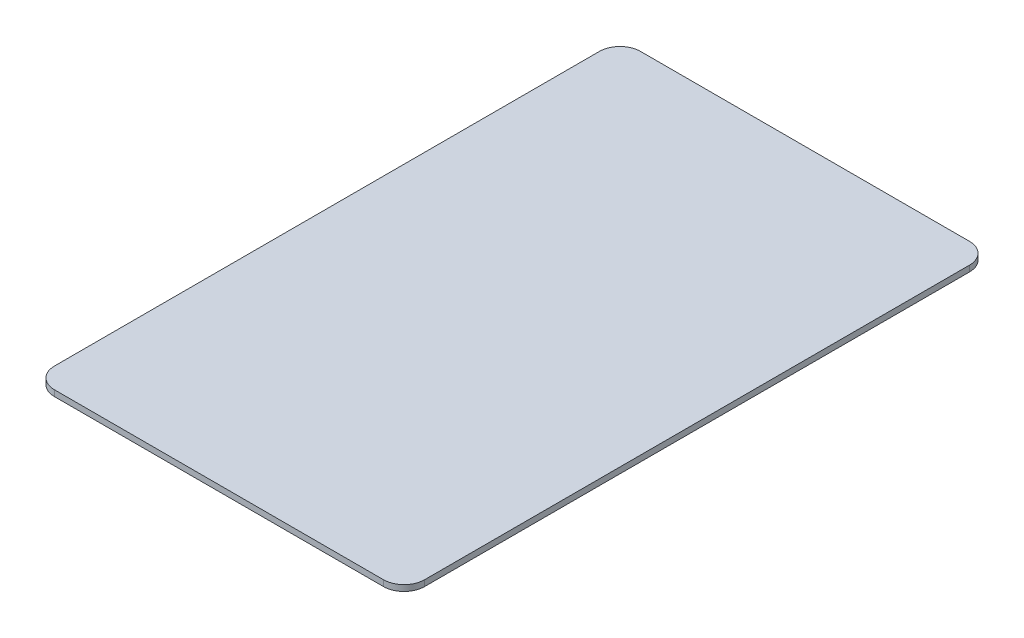
SolidWorks part; units mm, degrees
ref_plane "Front Plane" through (0, 0, 0) normal (0, 0, 1) x (1, 0, 0)
ref_plane "Top Plane" through (0, 0, 0) normal (0, 1, 0) x (1, 0, 0)
ref_plane "Right Plane" through (0, 0, 0) normal (1, 0, 0) x (0, 0, -1)
sketch "Sketch1" plane through (0, 0, 0) normal (0, 1, 0) x (1, 0, 0)
  line L1 (-24, -42.75) -> (24, -42.75)
  line L2 (-27, -39.75) -> (-27, 39.75)
  line L3 (-24, 42.75) -> (24, 42.75)
  line L4 (27, -39.75) -> (27, 39.75)
  line L5 (-27, -42.75) -> (27, 42.75) construction
  line L6 (-27, 42.75) -> (27, -42.75) construction
  arc A0 (24, 42.75) -> (27, 39.75) centre (24, 39.75) cw
  arc A1 (-24, -42.75) -> (-27, -39.75) centre (-24, -39.75) cw
  arc A2 (27, -39.75) -> (24, -42.75) centre (24, -39.75) cw
  arc A3 (-27, 39.75) -> (-24, 42.75) centre (-24, 39.75) cw
  point P0 (0, 0)
  dimension "D3" = 3
  dimension "D1" = 54
  dimension "D2" = 85.5
extrude "Boss-Extrude1" add sketch "Sketch1" along normal blind 0.87
